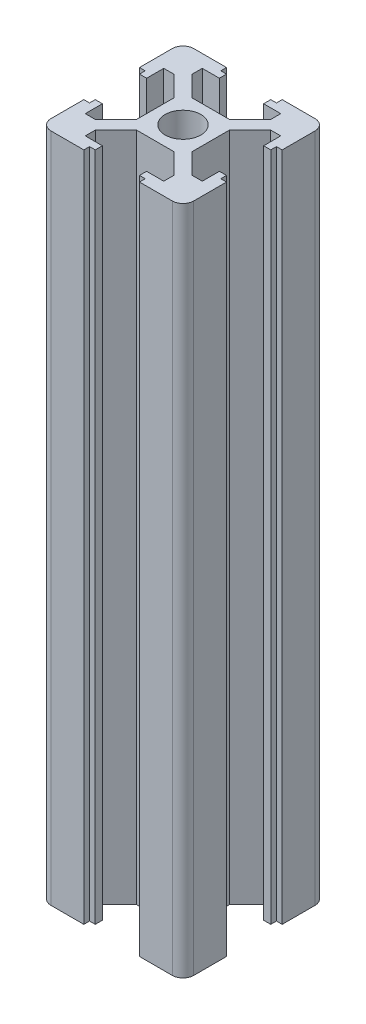
SolidWorks part; units mm, degrees
material "6063-O"
ref_plane "Front Plane" through (0, 0, 0) normal (0, 0, 1) x (1, 0, 0)
ref_plane "Top Plane" through (0, 0, 0) normal (0, 1, 0) x (1, 0, 0)
ref_plane "Right Plane" through (0, 0, 0) normal (1, 0, 0) x (0, 0, -1)
sketch "Sketch1" plane through (0, 0, 0) normal (0, 1, 0) x (1, 0, 0)
  line L0 (0, 14.5399) -> (0, 10) construction
  line L1 (-16.8658, 0) -> (2.5, 0) construction
  line L2 (13.2784, 3.9) -> (3.9, 3.9) construction
  line L3 (0, 0) -> (2.5, 0)
  line L4 (0, 0) -> (0, 2.5)
  line L5 (3.9, 10) -> (8.5, 10)
  line L6 (9.2, 0) -> (16.4291, 0) construction
  line L7 (-2.63, 3.9) -> (2.63, 3.9)
  line L9 (2.5491, 3.9) -> (2.63, 3.9)
  line L10 (3.9, 0) -> (3.9, 2.63)
  line L11 (13.2784, 3.1) -> (2.5491, 3.1) construction
  line L12 (8.2, 7.5573) -> (8.2, -3.0868) construction
  line L13 (9.2, 7.2593) -> (9.2, -8.1534) construction
  line L14 (10, 3.9) -> (9.2, 3.9)
  line L15 (9.2, 3.9) -> (9.2, 3.1)
  line L16 (9.2, 3.1) -> (8.2, 3.1)
  line L17 (8.2, 3.1) -> (8.2, 5.5)
  line L18 (8.2, 5.5) -> (6.77, 5.5)
  line L19 (6.77, 5.5) -> (3.9, 2.63)
  line L20 (5.0973, 5.5) -> (13.0082, 5.5) construction
  line L21 (3.1, 11.2046) -> (3.1, 2.6994) construction
  line L22 (3.9, 10.7498) -> (3.9, 3.9) construction
  line L23 (5.5, 11.523) -> (5.5, 1.4941) construction
  line L24 (-2.2597, 8.2) -> (6.1545, 8.2) construction
  line L25 (-2.9419, 9.2) -> (5.7225, 9.2) construction
  line L26 (3.9, 10) -> (3.9, 9.2)
  line L27 (3.9, 9.2) -> (3.1, 9.2)
  line L28 (3.1, 9.2) -> (3.1, 8.2)
  line L29 (3.1, 8.2) -> (5.5, 8.2)
  line L30 (5.5, 8.2) -> (5.5, 6.77)
  line L31 (5.5, 6.77) -> (2.63, 3.9)
  line L32 (0, 2.5) -> (0, -14.4122) construction
  line L33 (10, 3.9) -> (10, 8.5)
  line L34 (9.2, 0) -> (10, 0)
  line L35 (2.63, 3.9) -> (2.5491, 3.9) construction
  line L36 (3.9, 2.63) -> (3.9, 2.0627) construction
  line L37 (10, -3.9) -> (10, -8.5)
  line L38 (3.9, -10) -> (8.5, -10)
  line L39 (3.9, -10) -> (3.9, -9.2)
  line L40 (3.9, -9.2) -> (3.1, -9.2)
  line L41 (3.1, -9.2) -> (3.1, -8.2)
  line L42 (3.1, -8.2) -> (5.5, -8.2)
  line L43 (5.5, -8.2) -> (5.5, -6.77)
  line L44 (5.5, -6.77) -> (2.63, -3.9)
  line L45 (0, -3.9) -> (2.63, -3.9)
  line L46 (3.9, 0) -> (3.9, -2.63)
  line L47 (6.77, -5.5) -> (3.9, -2.63)
  line L48 (8.2, -5.5) -> (6.77, -5.5)
  line L49 (8.2, -3.1) -> (8.2, -5.5)
  line L50 (9.2, -3.1) -> (8.2, -3.1)
  line L51 (9.2, -3.9) -> (9.2, -3.1)
  line L52 (10, -3.9) -> (9.2, -3.9)
  line L53 (-3.9, -10) -> (-8.5, -10)
  line L54 (-10, -3.9) -> (-10, -8.5)
  line L55 (-10, -3.9) -> (-9.2, -3.9)
  line L56 (-9.2, -3.9) -> (-9.2, -3.1)
  line L57 (-9.2, -3.1) -> (-8.2, -3.1)
  line L58 (-8.2, -3.1) -> (-8.2, -5.5)
  line L59 (-8.2, -5.5) -> (-6.77, -5.5)
  line L60 (-6.77, -5.5) -> (-3.9, -2.63)
  line L61 (-3.9, 0) -> (-3.9, -2.63)
  line L62 (0, -3.9) -> (-2.63, -3.9)
  line L63 (-5.5, -6.77) -> (-2.63, -3.9)
  line L64 (-5.5, -8.2) -> (-5.5, -6.77)
  line L65 (-3.1, -8.2) -> (-5.5, -8.2)
  line L66 (-3.1, -9.2) -> (-3.1, -8.2)
  line L67 (-3.9, -9.2) -> (-3.1, -9.2)
  line L68 (-3.9, -10) -> (-3.9, -9.2)
  line L69 (-10, 3.9) -> (-10, 8.5)
  line L70 (-3.9, 10) -> (-8.5, 10)
  line L71 (-3.9, 10) -> (-3.9, 9.2)
  line L72 (-3.9, 9.2) -> (-3.1, 9.2)
  line L73 (-3.1, 9.2) -> (-3.1, 8.2)
  line L74 (-3.1, 8.2) -> (-5.5, 8.2)
  line L75 (-5.5, 8.2) -> (-5.5, 6.77)
  line L76 (-5.5, 6.77) -> (-2.63, 3.9)
  line L78 (-3.9, 0) -> (-3.9, 2.63)
  line L79 (-6.77, 5.5) -> (-3.9, 2.63)
  line L80 (-8.2, 5.5) -> (-6.77, 5.5)
  line L81 (-8.2, 3.1) -> (-8.2, 5.5)
  line L82 (-9.2, 3.1) -> (-8.2, 3.1)
  line L83 (-9.2, 3.9) -> (-9.2, 3.1)
  line L84 (-10, 3.9) -> (-9.2, 3.9)
  line L85 (0, 3.9) -> (-2.63, 3.9) [skipped]
  circle A0 centre (0, 0) radius 2.5
  arc A1 (8.5, 10) -> (10, 8.5) centre (8.5, 8.5) cw
  arc A2 (10, -8.5) -> (8.5, -10) centre (8.5, -8.5) cw
  arc A4 (-8.5, -10) -> (-10, -8.5) centre (-8.5, -8.5) cw
  arc A6 (-10, 8.5) -> (-8.5, 10) centre (-8.5, 8.5) cw
  point P12 (10, 10)
  point P126 (0, 0)
  dimension "D3" = 5
  dimension "D4" = 1.5
  dimension "D1" = 10
  dimension "D2" = 10
  dimension "D6" = 3.9
  dimension "D7" = 3.9
  dimension "D8" = 3.1
  dimension "D9" = 4
  dimension "D11" = 5.5
  dimension "D12" = 1.8
  dimension "D13" = 0.8
  dimension "D14" = 3.9
  dimension "D15" = 3.1
  dimension "D16" = 5.5
  dimension "D17" = 1.27
  dimension "D18" = 1.27
  dimension "D19" = 1.27
  dimension "D20" = 1.27
extrude "Boss-Extrude1" add sketch "Sketch1" along normal blind 94 contours A6 L69 L84 L83 L82 L81 L80 L79 L78 L61 L60 L59 L58 L57 L56 L55 L54 A4 L53 L68 L67 L66 L65 L64 L63 L62 L45 L44 L43 L42 L41 L40 L39 L38 A2 L37 L52 L51 L50 L49 L48 L47 L46 L10 L19 L18 L17 L16 L15 L14 L33
